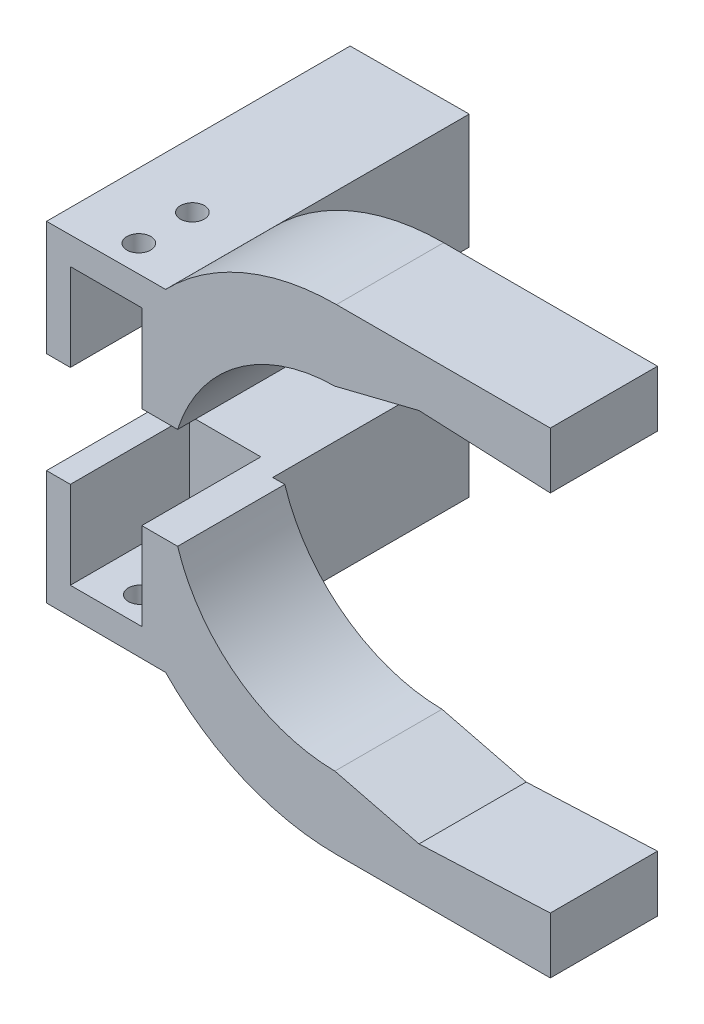
SolidWorks part; units mm, degrees
ref_plane "Front Plane" through (0, 0, 0) normal (0, 0, 1) x (1, 0, 0)
ref_plane "Top Plane" through (0, 0, 0) normal (0, 1, 0) x (1, 0, 0)
ref_plane "Right Plane" through (0, 0, 0) normal (1, 0, 0) x (0, 0, -1)
sketch "Sketch1" plane through (0, 0, 0) normal (0, 0, 1) x (1, 0, 0)
  line L0 (0, 68.5) -> (60, 68.5)
  line L1 (0, 0) -> (0, 68.5) construction
  line L2 (0, 83.5) -> (60, 83.5)
  line L3 (0, 0) -> (15.3217, 0)
  line L4 (60, 68.5) -> (60, 83.5)
  line L5 (0, -83.5) -> (60, -83.5)
  line L6 (0, -68.5) -> (60, -68.5)
  line L7 (60, -83.5) -> (60, -68.5)
  line L8 (0, 55) -> (60, 55) construction
  line L9 (0, -55) -> (60, -55) construction
  line L10 (0, 0) -> (0, -13.5) construction
  line L11 (0, -13.5) -> (-82.4015, -13.5) construction
  line L12 (0, -8.5) -> (-103.3556, -8.5) construction
  line L13 (-103.3556, 21.5) -> (-83.3556, 21.5)
  line L14 (-103.3556, 21.5) -> (-82.4015, 21.5) construction
  line L15 (0, 13.5) -> (-103.3556, 13.5) construction
  line L16 (0, 8.5) -> (-103.3556, 8.5) construction
  line L17 (-83.3556, 8.5) -> (-103.3556, 8.5)
  line L18 (-103.3556, 8.5) -> (-103.3556, 13.5)
  line L19 (-103.3556, 13.5) -> (-82.4015, 13.5)
  line L20 (-83.3556, 8.5) -> (-67.9706, 8.5)
  line L21 (-83.3556, -8.5) -> (-103.3556, -8.5)
  line L22 (-103.3556, -8.5) -> (-103.3556, -13.5)
  line L23 (-103.3556, -13.5) -> (-83.3556, -13.5)
  line L24 (-103.3556, 27.5) -> (-84.0671, 27.5)
  line L25 (-103.3556, 27.5) -> (-80.6846, 27.5) construction
  line L26 (-103.3556, 21.5) -> (-103.3556, 27.5)
  line L27 (-103.3556, -8.5) -> (-103.3556, -13.5)
  line L28 (-103.3556, -27.5) -> (-84.0671, -27.5)
  line L29 (-103.3556, -21.5) -> (-103.3556, -27.5)
  line L30 (-103.3556, -21.5) -> (-83.3556, -21.5)
  line L31 (-103.3556, -13.5) -> (-83.3556, -13.5)
  line L32 (-83.3556, -8.5) -> (-67.9706, -8.5)
  line L33 (-83.3556, 13.5) -> (-83.3556, 21.5)
  line L34 (-83.3556, -13.5) -> (-83.3556, -21.5)
  line L35 (-83.3556, 21.5) -> (-83.3556, 13.5)
  line L36 (-83.3556, -13.5) -> (-83.3556, -21.5)
  line L41 (-83.3556, -13.5) -> (-103.3556, -13.5) construction
  line L44 (-103.3556, 21.5) -> (-80.6846, 21.5) construction
  arc A0 (0, 55) -> (-54.3392, 8.5) centre (0, 0) ccw construction
  arc A4 (0, 68.5) -> (-67.9706, 8.5) centre (0, 0) ccw
  arc A5 (0, 83.5) -> (-77.0532, 32.1722) centre (0, 0) ccw
  circle A6 centre (0, 0) radius 83.5 construction
  circle A7 centre (0, 0) radius 68.5 construction
  arc A8 (0, 55) -> (-54.3392, 8.5) centre (0, 0) ccw construction
  arc A9 (-54.3392, -8.5) -> (0, -55) centre (0, 0) ccw construction
  arc A10 (-54.3392, -8.5) -> (0, -55) centre (0, 0) ccw construction
  arc A11 (0, 55) -> (0, -55) centre (0, 0) ccw construction
  arc A12 (-67.9706, -8.5) -> (0, -68.5) centre (0, 0) ccw
  arc A13 (0, 68.5) -> (0, -68.5) centre (0, 0) ccw construction
  arc A14 (-77.0532, 32.1722) -> (-84.0671, 27.5) centre (-84.0671, 35.1007) cw
  arc A16 (-77.0532, -32.1722) -> (0, -83.5) centre (0, 0) ccw
  arc A17 (-77.0532, -32.1722) -> (-84.0671, -27.5) centre (-84.0671, -35.1007) ccw
  dimension "D1" = 17
  dimension "D2" = 15
  dimension "D3" = 68.5
  dimension "D4" = 60
  dimension "D6" = 13.5
  dimension "D7" = 20
  dimension "D8" = 8
  dimension "D9" = 6
  dimension "D5" = 13.5
extrude "Boss-Extrude1" add sketch "Sketch1" along normal blind 18
sketch "Sketch3" plane through (0, -27.5, 0) normal (0, -1, 0) x (1, 0, 0)
  line L0 (-84.0671, 18) -> (-84.0671, 9) construction
  line L1 (-84.0671, 18) -> (-84.0671, 0) construction
  line L2 (-84.0671, 9) -> (-88.5671, 9) construction
  line L3 (-88.5671, 9) -> (-97.5671, 9) construction
  circle A0 centre (-88.5671, 9) radius 2
  circle A1 centre (-97.5671, 9) radius 2
  dimension "D2" = 4
  dimension "D3" = 4
  dimension "D1" = 4.5
  dimension "D4" = 9
extrude "Cut-Extrude2" cut sketch "Sketch3" against normal up to surface (55 mm away) up to face at (-93.7114, 27.5, 9)
sketch "Sketch4" plane through (-103.3556, 0, 0) normal (-1, 0, 0) x (0, 0, 1)
  line L0 (9, 27.5) -> (9, 21.5) construction
  line L1 (18, 27.5) -> (0, 27.5) construction
  line L2 (18, 21.5) -> (0, 21.5) construction
  line L3 (9, 24.5) -> (4, 24.5) construction
  line L4 (4, 27.5) -> (4, 21.5)
  line L5 (18, 27.5) -> (0, 27.5) construction
  line L6 (18, 21.5) -> (0, 21.5) construction
  line L7 (4, 21.5) -> (0, 21.5)
  line L8 (0, 21.5) -> (0, 27.5)
  line L9 (0, 27.5) -> (4, 27.5)
  line L10 (14, 21.5) -> (18, 21.5)
  line L11 (18, 21.5) -> (18, 27.5)
  line L12 (18, 27.5) -> (14, 27.5)
  line L13 (14, 27.5) -> (14, 21.5)
sketch "Sketch5" plane through (0, 21.5, 0) normal (0, -1, 0) x (1, 0, 0)
  line L0 (-103.3556, 14) -> (-84.0671, 14)
  line L1 (-103.3556, 18) -> (-103.3556, 14) construction
  line L2 (-103.3556, 18) -> (-103.3556, 0) construction
  line L3 (-84.0671, 18) -> (-84.0671, 0) construction
  line L6 (-103.3556, 18) -> (-103.3556, 14)
  line L7 (-103.3556, 4) -> (-103.3556, 0)
  line L8 (-103.3556, 0) -> (-103.3556, 4) construction
  line L9 (-103.3556, 0) -> (-84.0671, 0)
  line L11 (-84.0671, 4) -> (-103.3556, 4)
  line L12 (-103.3556, 18) -> (-83.3556, 18)
  line L13 (-83.3556, 18) -> (-83.3556, 14)
  line L14 (-83.3556, 14) -> (-84.0671, 14)
  line L15 (-84.0671, 4) -> (-83.3556, 4)
  line L16 (-83.3556, 4) -> (-83.3556, 0)
  line L17 (-83.3556, 0) -> (-84.0671, 0)
  dimension "D1" = 4
  dimension "D2" = 4
extrude "Boss-Extrude3" add sketch "Sketch5" along normal up to surface (8 mm away) up to face at (-88.5671, 13.5, 11)
sketch "Sketch6" plane through (0, -13.5, 0) normal (0, -1, 0) x (-1, 0, 0)
  line L0 (103.3556, -18) -> (83.3556, -18)
  line L1 (83.3556, -18) -> (83.3556, -14)
  line L2 (83.3556, -14) -> (103.3556, -14)
  line L3 (103.3556, -14) -> (103.3556, -18)
  line L4 (83.3556, -18) -> (103.3556, -18)
  line L5 (84.0671, -9) -> (85.651, -9) construction
  line L6 (84.0671, -18) -> (84.0671, 0) construction
  line L7 (83.3556, 0) -> (83.3556, -4)
  line L8 (103.3556, 0) -> (83.3556, 0)
  line L9 (103.3556, -4) -> (103.3556, 0)
  line L10 (83.3556, -4) -> (103.3556, -4)
  line M8 (103.3556, 0) -> (83.3556, 0)
  line M9 (83.3556, 0) -> (83.3556, -18)
  line M10 (83.3556, -18) -> (103.3556, -18)
  line M11 (103.3556, -18) -> (103.3556, 0)
  dimension "D1" = 4
extrude "Boss-Extrude4" add sketch "Sketch6" along normal up to surface (8 mm away) contours L2 M9 M10 M11 | L10 M9 M11 M8 up to face at (-90.5671, -21.5, 9)
sketch "Sketch7" plane through (0, 0, 0) normal (0, 0, -1) x (-1, 0, 0)
  line L0 (67.9706, -8.5) -> (103.3556, -8.5)
  line L1 (103.3556, -8.5) -> (103.3556, -27.5)
  line L2 (103.3556, -27.5) -> (62.7375, -27.5)
  line L3 (0, 0) -> (137.0537, 0) construction
  line L4 (103.3556, 27.5) -> (62.7375, 27.5)
  line L5 (103.3556, 8.5) -> (103.3556, 27.5)
  line L6 (67.9706, 8.5) -> (103.3556, 8.5)
  arc A0 (0, -68.5) -> (67.9706, -8.5) centre (0, 0) ccw construction
  arc A1 (67.9706, -8.5) -> (62.7375, -27.5) centre (0, 0) cw
  arc A2 (67.9706, 8.5) -> (62.7375, 27.5) centre (0, 0) ccw
extrude "Boss-Extrude5" add sketch "Sketch7" along normal blind 33
sketch "Sketch9" plane through (0, 0, 18) normal (0, 0, 1) x (1, 0, 0)
  line L0 (-67.9706, 8.5) -> (-53.3268, 8.5)
  line L2 (60, 68.5) -> (60, 54)
  line L3 (60, 54) -> (0, 54)
  line L4 (60, 68.5) -> (0, 68.5)
  line L5 (0, -54) -> (60, -54)
  line L6 (60, -54) -> (60, -68.5)
  line L7 (60, -68.5) -> (0, -68.5)
  line L8 (-67.9706, -8.5) -> (-53.3268, -8.5)
  arc A0 (0, 54) -> (-53.3268, 8.5) centre (0, 0) ccw
  arc A1 (0, 68.5) -> (-67.9706, 8.5) centre (0, 0) ccw
  arc A2 (-67.9706, -8.5) -> (0, -68.5) centre (0, 0) ccw
  arc A3 (-53.3268, -8.5) -> (0, -54) centre (0, 0) ccw
  dimension "D1" = 108
extrude "Boss-Extrude6" add sketch "Sketch9" against normal up to surface (18 mm away) up to face at (-16.7173, 58.7299, 0)
sketch "Sketch10" plane through (0, 0, 18) normal (0, 0, 1) x (1, 0, 0)
  line L0 (-77.0532, 32.1722) -> (-66.0848, 32.1722)
  line L1 (50, 73.5) -> (60, 73.5)
  line L2 (0, 0) -> (-21.6778, 0)
  line L3 (-78.2189, 18.5) -> (-78.2189, 18.5)
  line L4 (-78.2189, 18.5) -> (-78.2189, 18.5)
  line L6 (-103.3556, 8.5) -> (-53.3268, 8.5)
  line L7 (0, 54) -> (60, 54)
  line L8 (60, 54) -> (60, 83.5)
  line L9 (60, 83.5) -> (0, 83.5)
  line L10 (-84.0671, 27.5) -> (-103.3556, 27.5)
  line L11 (-103.3556, 27.5) -> (-103.3556, 8.5)
  line L12 (-103.3556, 8.5) -> (-53.3268, 8.5)
  line L13 (0, 54) -> (60, 54)
  line L14 (60, 54) -> (60, 83.5)
  line L15 (60, 83.5) -> (0, 83.5)
  line L16 (-84.0671, 27.5) -> (-103.3556, 27.5)
  line L17 (-103.3556, 27.5) -> (-103.3556, 8.5)
  line L20 (50, 73.5) -> (0, 73.5)
  line L21 (-78.2189, 18.5) -> (-61.2679, 18.5) construction
  line L22 (0, 64) -> (50, 64) construction
  line L23 (50, 64) -> (50, 73.5) construction
  line L24 (60, -83.5) -> (0, -83.5)
  line L25 (60, -54) -> (60, -83.5)
  line L26 (50, -73.5) -> (60, -73.5)
  line L27 (50, -73.5) -> (0, -73.5)
  line L28 (-77.0532, -32.1722) -> (-66.0848, -32.1722)
  line L29 (60, -54) -> (0, -54) construction
  line L30 (-103.3556, -8.5) -> (-53.3268, -8.5) construction
  line L31 (60, -54) -> (0, -54)
  line L32 (-103.3556, -8.5) -> (-53.3268, -8.5)
  line L33 (0, -56) -> (60, -56)
  line L34 (0, 56) -> (60, 56)
  line L35 (-53.3268, -8.5) -> (-55.3512, -8.5)
  arc A0 (0, 73.5) -> (-67.8253, 28.3192) centre (0, 0) ccw construction
  arc A1 (0, -73.5) -> (-66.0848, -32.1722) centre (0, 0) cw
  arc A2 (0, 73.5) -> (-66.0848, 32.1722) centre (0, 0) ccw
  arc A3 (0, 54) -> (-53.3268, 8.5) centre (0, 0) ccw
  arc A4 (0, 83.5) -> (-77.0532, 32.1722) centre (0, 0) ccw
  arc A5 (-84.0671, 27.5) -> (-77.0532, 32.1722) centre (-84.0671, 35.1007) ccw
  arc A6 (0, 54) -> (-53.3268, 8.5) centre (0, 0) ccw
  arc A7 (0, 83.5) -> (-77.0532, 32.1722) centre (0, 0) ccw
  arc A8 (-84.0671, 27.5) -> (-77.0532, 32.1722) centre (-84.0671, 35.1007) ccw
  arc A11 (-78.2189, 18.5) -> (-67.8253, 28.3192) centre (-84.0671, 35.1007) ccw construction
  arc A12 (0, 64) -> (-61.2679, 18.5) centre (0, 0) ccw construction
  arc A13 (0, -83.5) -> (-77.0532, -32.1722) centre (0, 0) cw
  arc A14 (-55.3512, -8.5) -> (0, -56) centre (0, 0) ccw
  arc A15 (-53.3268, -8.5) -> (0, -54) centre (0, 0) ccw construction
  arc A16 (-53.3268, -8.5) -> (0, -54) centre (0, 0) ccw
  arc A17 (0, 56) -> (-55.3512, 8.5) centre (0, 0) ccw
  arc A18 (-55.3512, -8.5) -> (0, -56) centre (0, 0) ccw
  arc A19 (0, 56) -> (-55.3512, 8.5) centre (0, 0) ccw
  arc M15 (-53.3268, 8.5) -> (0, 54) centre (0, 0) cw
  line M16 (0, 54) -> (60, 54)
  line M17 (60, 54) -> (60, 83.5)
  line M18 (60, 83.5) -> (0, 83.5)
  arc M19 (0, 83.5) -> (-77.0532, 32.1722) centre (0, 0) ccw
  dimension "D1" = 0
  dimension "D2" = 10
extrude "Cut-Extrude3" cut sketch "Sketch10" against normal up to surface (18 mm away) contours A2 L20 L1 L0 M17 M18 M19 | A13 L24 L25 L26 L27 A1 L28 | A16 L32 A14 L33 L25 L31 | L34 A17 L12 M15 M16 M17 up to face at (-26.8097, -44.4207, 0)
fillet "Fillet1" radius 5 1 edges at (-77.0532, 32.1722, 9)
sketch "Sketch12" plane through (0, 0, 18) normal (0, 0, 1) x (1, 0, 0)
  line L0 (0, 0) -> (-7.8937, 0)
  line L1 (-77.0532, -32.1722) -> (-66.0848, -32.1722) construction
  line L2 (-74.2734, 32.1722) -> (-66.0848, 32.1722) construction
  line L3 (-77.0532, -32.1722) -> (-66.0848, -32.1722)
  line L4 (-74.2734, 32.1722) -> (-66.0848, 32.1722)
  arc A0 (-84.0671, 27.5) -> (-66.0848, 32.1722) centre (-82.8641, 59.811) ccw
  arc A1 (-84.0671, -27.5) -> (-66.0848, -32.1722) centre (-82.8641, -59.811) cw
  arc A2 (-77.0532, -32.1722) -> (-84.0671, -27.5) centre (-84.0671, -35.1007) ccw construction
  arc A3 (-74.2734, 32.1722) -> (-78.1596, 30.3183) centre (-74.2734, 27.1722) ccw construction
  arc A4 (-84.0671, 27.5) -> (-78.1596, 30.3183) centre (-84.0671, 35.1007) ccw construction
  arc A5 (-77.0532, -32.1722) -> (-84.0671, -27.5) centre (-84.0671, -35.1007) ccw
  arc A6 (-74.2734, 32.1722) -> (-78.1596, 30.3183) centre (-74.2734, 27.1722) ccw
  arc A7 (-84.0671, 27.5) -> (-78.1596, 30.3183) centre (-84.0671, 35.1007) ccw
  line M2 (-66.0848, 32.1722) -> (-74.2734, 32.1722)
  arc M3 (-74.2734, 32.1722) -> (-78.1596, 30.3183) centre (-74.2734, 27.1722) ccw
  arc M4 (-78.1596, 30.3183) -> (-84.0671, 27.5) centre (-84.0671, 35.1007) cw
extrude "Cut-Extrude4" cut sketch "Sketch12" against normal up to surface (18 mm away) contours A0 M4 M2 M3 | A1 L3 A5 up to face at (-30.7967, -41.4201, 0)
sketch "Sketch13" plane through (0, 0, 18) normal (0, 0, 1) x (1, 0, 0)
  line L0 (0, 28) -> (35.922, 28)
  line L2 (0, -28) -> (35.922, -28)
  line L3 (0, 40) -> (35.922, 40)
  line L4 (0, -40) -> (35.922, -40)
  line L5 (-103.3556, 27.5) -> (-28.7012, 27.8612)
  line L6 (-103.3556, 8.5) -> (-39.0864, 8.5)
  line L7 (-0.2709, 27.9987) -> (0, 28)
  line L8 (-59.0864, -8.5) -> (-59.0864, -27.7142)
  line L9 (-103.3556, -8.5) -> (-103.3556, -27.5)
  line L10 (-103.3556, -27.5) -> (-28.7012, -27.8612)
  line L11 (-0.2709, -27.9987) -> (0, -28)
  line L12 (-39.0864, -8.5) -> (-59.0864, -8.5)
  line L13 (-59.0864, -27.7142) -> (-28.7012, -27.8612)
  line L14 (-39.0864, 8.5) -> (-59.0864, 8.5)
  line L15 (-59.0864, 8.5) -> (-59.0864, 27.7142)
  line L16 (-59.0864, 27.7142) -> (-28.7012, 27.8612)
  line L17 (-39.0864, 8.5) -> (-26.6786, 8.5)
  line L18 (-39.0864, -8.5) -> (-26.6786, -8.5)
  line L19 (35.922, 40) -> (35.922, 28)
  line L20 (35.922, -28) -> (35.922, -40)
  arc A0 (0, 28) -> (-26.6786, 8.5) centre (0, 0) ccw
  arc A1 (0, 40) -> (-28.7012, 27.8612) centre (0, 0) ccw
  arc A2 (-28.7012, -27.8612) -> (0, -40) centre (0, 0) ccw
  arc A3 (0, 40) -> (0, -40) centre (0, 0) ccw construction
  arc A4 (-26.6786, -8.5) -> (0, -28) centre (0, 0) ccw
  arc A5 (0, 28) -> (0, -28) centre (0, 0) ccw construction
  arc M7 (0, -56) -> (-55.3512, -8.5) centre (0, 0) cw
  dimension "D1" = 56
  dimension "D3" = 20
  dimension "D2" = 12
extrude "Boss-Extrude7" add sketch "Sketch13" against normal blind 18 contours L3 A1 L5 L15 L6 L17 A0 L0 L19 | A4 L18 L12 L10 A2 L4 L20 L2 M7
sketch "Sketch14" plane through (0, 0, 18) normal (0, 0, 1) x (1, 0, 0)
  line L0 (35.922, -28) -> (35.922, -40) construction
  line L1 (0, -40) -> (35.922, -40) construction
  line L2 (0, -28) -> (35.922, -28) construction
  line L3 (-103.3556, -27.5) -> (-28.7012, -27.8612) construction
  line L4 (-59.0864, -8.5) -> (-59.0864, -27.7142) construction
  line L5 (-39.0864, -8.5) -> (-26.6786, -8.5) construction
  line L6 (-39.0864, -8.5) -> (-59.0864, -8.5) construction
  line L7 (35.922, 40) -> (35.922, 28) construction
  line L8 (0, 28) -> (35.922, 28) construction
  line L9 (-39.0864, 8.5) -> (-26.6786, 8.5) construction
  line L10 (-103.3556, 8.5) -> (-39.0864, 8.5) construction
  line L11 (-59.0864, 8.5) -> (-59.0864, 27.7142) construction
  line L12 (0, 40) -> (35.922, 40) construction
  line L13 (-103.3556, 27.5) -> (-28.7012, 27.8612) construction
  line L14 (35.922, -28) -> (35.922, -40)
  line L15 (0, -40) -> (35.922, -40)
  line L16 (0, -28) -> (35.922, -28)
  line L17 (-103.3556, -27.5) -> (-28.7012, -27.8612)
  line L18 (-59.0864, -8.5) -> (-59.0864, -27.7142)
  line L19 (-39.0864, -8.5) -> (-26.6786, -8.5)
  line L20 (-39.0864, -8.5) -> (-59.0864, -8.5)
  line L21 (35.922, 40) -> (35.922, 28)
  line L22 (0, 28) -> (35.922, 28)
  line L23 (-39.0864, 8.5) -> (-26.6786, 8.5)
  line L24 (-103.3556, 8.5) -> (-39.0864, 8.5)
  line L25 (-59.0864, 8.5) -> (-59.0864, 27.7142)
  line L26 (0, 40) -> (35.922, 40)
  line L27 (-103.3556, 27.5) -> (-28.7012, 27.8612)
  line L28 (-103.3556, 27.5) -> (-103.3556, 83.7359)
  line L29 (-103.3556, 83.7359) -> (76.4268, 83.7359)
  line L30 (76.4268, 83.7359) -> (76.4268, 40)
  line L31 (76.4268, 40) -> (35.922, 40)
  line L32 (-59.0864, -8.5) -> (-103.3556, -8.5)
  line L33 (-103.3556, -8.5) -> (-103.3556, -78.5297)
  line L34 (-103.3556, -78.5297) -> (60, -73.5)
  line L35 (60, -73.5) -> (60, -40)
  line L36 (60, -40) -> (35.922, -40)
  arc A0 (-28.7012, -27.8612) -> (0, -40) centre (0, 0) ccw construction
  arc A1 (-26.6786, -8.5) -> (0, -28) centre (0, 0) ccw construction
  arc A2 (0, 28) -> (-26.6786, 8.5) centre (0, 0) ccw construction
  arc A3 (0, 40) -> (-28.7012, 27.8612) centre (0, 0) ccw construction
  arc A4 (-28.7012, -27.8612) -> (0, -40) centre (0, 0) ccw
  arc A5 (-26.6786, -8.5) -> (0, -28) centre (0, 0) ccw
  arc A6 (0, 28) -> (-26.6786, 8.5) centre (0, 0) ccw
  arc A7 (0, 40) -> (-28.7012, 27.8612) centre (0, 0) ccw
  arc M2 (-84.0671, -27.5) -> (-66.0848, -32.1722) centre (-82.8641, -59.811) cw
  arc M3 (-66.0848, -32.1722) -> (0, -73.5) centre (0, 0) ccw
  line M5 (60, -73.5) -> (60, -56)
  line M6 (60, -56) -> (0, -56)
  arc M7 (0, -56) -> (-48.6325, -27.7647) centre (0, 0) cw
  line M8 (-48.6325, -27.7647) -> (-28.7012, -27.8612)
  arc M9 (-28.7012, -27.8612) -> (0, -40) centre (0, 0) ccw
  line M10 (0, -40) -> (35.922, -40)
extrude "Cut-Extrude6" cut sketch "Sketch14" against normal blind 18 contours L35 L36 M10 M9 M8 M7 M6 | L34 L17 M3 M5 M6 M7 M2 | L33 L34 L17 M3 M2 | A7 L26 L31 L30 L29 L28 L27
sketch "Sketch16" plane through (0, 0, 18) normal (0, 0, 1) x (1, 0, 0)
  line L0 (-28.7012, -27.8612) -> (-59.0864, -27.7142)
  line L3 (-103.3556, -8.5) -> (-26.6786, -8.5) construction
  line L4 (-96.5111, -8.5) -> (-96.5111, -27.5331)
  line L5 (-103.3556, -27.5) -> (-28.7012, -27.8612) construction
  line L6 (-96.5111, -27.5331) -> (-59.0864, -27.7142)
  line L7 (-28.7012, -27.8612) -> (-48.7012, -27.7644)
  line L8 (-48.7012, -27.7644) -> (-48.7012, 27.7644)
  line L9 (-103.3556, 27.5) -> (-28.7012, 27.8612) construction
  line L10 (-48.7012, 27.7644) -> (-96.5111, 27.5331)
  line L11 (-96.5111, 27.5331) -> (-96.5111, -27.5331)
  line L12 (-48.7012, -27.7644) -> (-96.5111, -27.5331)
  arc M2 (-84.0671, -27.5) -> (-79.9033, -27.6135) centre (-82.8641, -59.811) cw
  line M3 (-79.9033, -27.6135) -> (-28.7012, -27.8612)
  line M9 (-26.6786, -8.5) -> (-103.3556, -8.5)
  line M11 (-103.3556, -27.5) -> (-84.0671, -27.5)
  dimension "D1" = 20
extrude "Cut-Extrude8" cut sketch "Sketch16" against normal up to surface (51 mm away) contours L10 L11 L8 M9 | L8 L4 M3 M9 M11 M2 up to face at (-84.5265, -18.0473, -33)
sketch "Sketch17" plane through (0, 0, 0) normal (0, 0, -1) x (-1, 0, 0)
  line L0 (28.7012, 27.8612) -> (28.7012, 8.5)
  line L1 (39.0864, 8.5) -> (26.6786, 8.5) construction
  line L2 (28.7012, 8.5) -> (48.7012, 8.5)
  line L3 (48.7012, 8.5) -> (48.7012, 27.7644)
  line L4 (48.7012, 27.7644) -> (28.7012, 27.8612)
  line L5 (0, 0) -> (6.9369, 0) construction
  line L6 (28.7012, -8.5) -> (48.7012, -8.5)
  line L7 (48.7012, -8.5) -> (48.7012, -27.7644)
  line L8 (48.7012, -27.7644) -> (28.7012, -27.8612)
  line L9 (28.7012, -27.8612) -> (28.7012, -8.5)
  line M6 (28.7012, -27.8612) -> (48.7012, -27.7644)
  line M7 (48.7012, -27.7644) -> (48.7012, -8.5)
  line M8 (48.7012, -8.5) -> (26.6786, -8.5)
extrude "Boss-Extrude9" add sketch "Sketch17" along normal blind 33 contours L3 L4 L0 L2 | L9 M6 M7 M8
sketch "Sketch18" plane through (0, 0, 18) normal (0, 0, 1) x (1, 0, 0)
  line L0 (-48.7012, 27.7644) -> (-116.673, 35.4757)
  line L1 (-116.673, 35.4757) -> (-116.673, -41.632)
  line L2 (-116.673, -41.632) -> (-48.7012, -27.7644)
  line L3 (-48.7012, -27.7644) -> (-48.7012, 27.7644)
extrude "Cut-Extrude9" cut sketch "Sketch18" against normal up to surface (51 mm away) up to face at (-38.7012, 18.1564, -33)
sketch "Sketch24" plane through (0, 0, 18) normal (0, 0, 1) x (1, 0, 0)
  line L0 (0, 0) -> (-8.3535, 0) construction
  line L1 (-44.7012, -13.1806) -> (-32.7012, -13.1806)
  line L2 (-28.7012, 18.1806) -> (-32.7012, 18.1806) construction
  line L3 (-32.7012, 13.1806) -> (-32.7012, 23.1806)
  line L4 (-32.7012, 23.1806) -> (-44.7012, 23.1806)
  line L5 (-44.7012, 23.1806) -> (-44.7012, 13.1806)
  line L6 (-44.7012, 13.1806) -> (-32.7012, 13.1806)
  line L7 (-103.3556, 27.5) -> (-28.7012, 27.8612) construction
  line L8 (-32.7012, -13.1806) -> (-32.7012, -23.1806)
  line L9 (-32.7012, -23.1806) -> (-44.7012, -23.1806)
  line L10 (-44.7012, -23.1806) -> (-44.7012, -13.1806)
  point P10 (-32.7012, 18.1806)
  dimension "D1" = 9.6611
  dimension "D2" = 10
  dimension "D3" = 12
extrude "Cut-Extrude13" cut sketch "Sketch24" against normal blind 20
sketch "Sketch27" plane through (-0.1355, 27.9993, 0) normal (-0.0048, 1, 0) x (1, 0.0048, 0)
  line L0 (-28.566, -18) -> (-32.566, -18) construction
  line L1 (-59.2198, -18) -> (-28.8356, -18) construction
  line L2 (-32.566, -18) -> (-42.566, -18) construction
  line L3 (-37.566, -18) -> (-37.566, -13.5) construction
  line L4 (-37.566, -13.5) -> (-37.566, -4.5) construction
  circle A0 centre (-37.566, -13.5) radius 2
  circle A1 centre (-37.566, -4.5) radius 2
  dimension "D1" = 4
  dimension "D2" = 9
  dimension "D3" = 4.5
extrude "Cut-Extrude14" cut sketch "Sketch27" against normal up to surface (55.6178 mm away)
sketch "Sketch28" plane through (0, 0, 18) normal (0, 0, 1) x (1, 0, 0)
  line L0 (-32.7012, 13.1806) -> (-32.7012, -13.1806)
  line L1 (-32.7012, -13.1806) -> (-44.7012, -13.1806)
  line L2 (-44.7012, -13.1806) -> (-44.7012, 13.1806)
  line L3 (-44.7012, 13.1806) -> (-32.7012, 13.1806)
extrude "Cut-Extrude15" cut sketch "Sketch28" against normal up to surface (20 mm away) up to face at (-38.7012, 18.1806, -2)
sketch "Sketch29" plane through (0, 0, 18) normal (0, 0, 1) x (1, 0, 0)
  line L9 (35.922, 28) -> (35.922, 30.548)
  line L10 (35.922, 40) -> (35.922, 28) construction
  line L11 (35.922, 30.548) -> (13.866, 31.5223)
  line L12 (13.866, 31.5223) -> (-0.2709, 27.9987)
  line L13 (0, 0) -> (6.8611, 0) construction
  line L14 (-0.2709, 27.9987) -> (35.922, 28)
  line L15 (35.922, -28) -> (35.922, -30.548)
  line L16 (-0.2709, -27.9987) -> (35.922, -28)
  line L17 (35.922, -30.548) -> (13.866, -31.5223)
  line L18 (13.866, -31.5223) -> (-0.2709, -27.9987)
extrude "Cut-Extrude16" cut sketch "Sketch29" against normal up to surface (18 mm away) contours L11 L12 L14 L9 | L17 L18 L16 L15 up to face at (-2.3787, 26.8752, 0)
